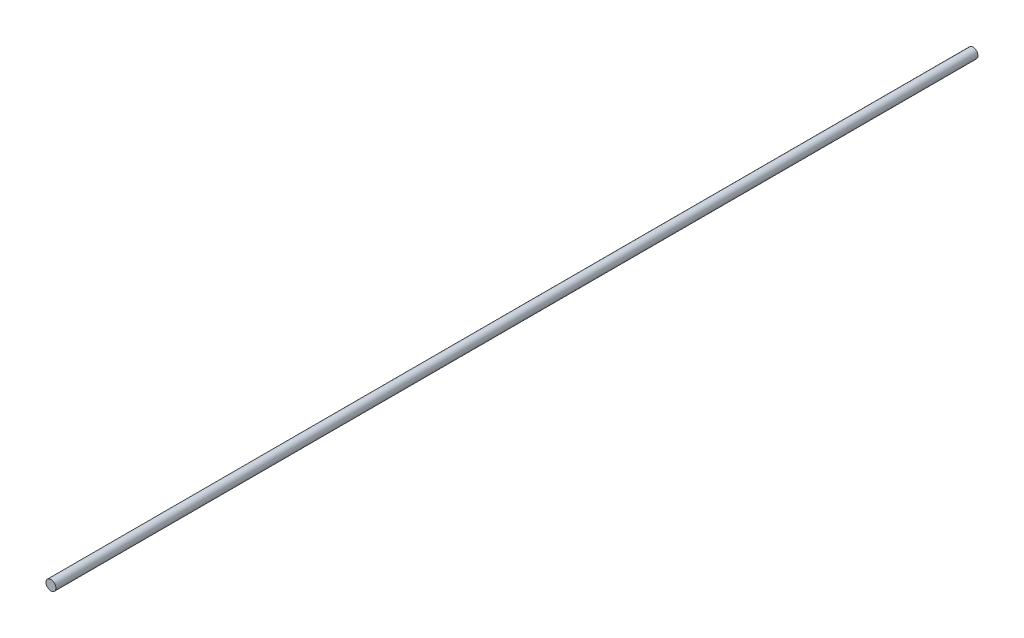
SolidWorks part; units mm, degrees
ref_plane "Front Plane" through (0, 0, 0) normal (0, 0, 1) x (1, 0, 0)
ref_plane "Top Plane" through (0, 0, 0) normal (0, 1, 0) x (1, 0, 0)
ref_plane "Right Plane" through (0, 0, 0) normal (1, 0, 0) x (0, 0, -1)
sketch "Sketch1" plane through (0, 0, 0) normal (0, 0, 1) x (1, 0, 0)
  circle A0 centre (0, 0) radius 1.5
extrude "Boss-Extrude1" add sketch "Sketch1" along normal blind 279
